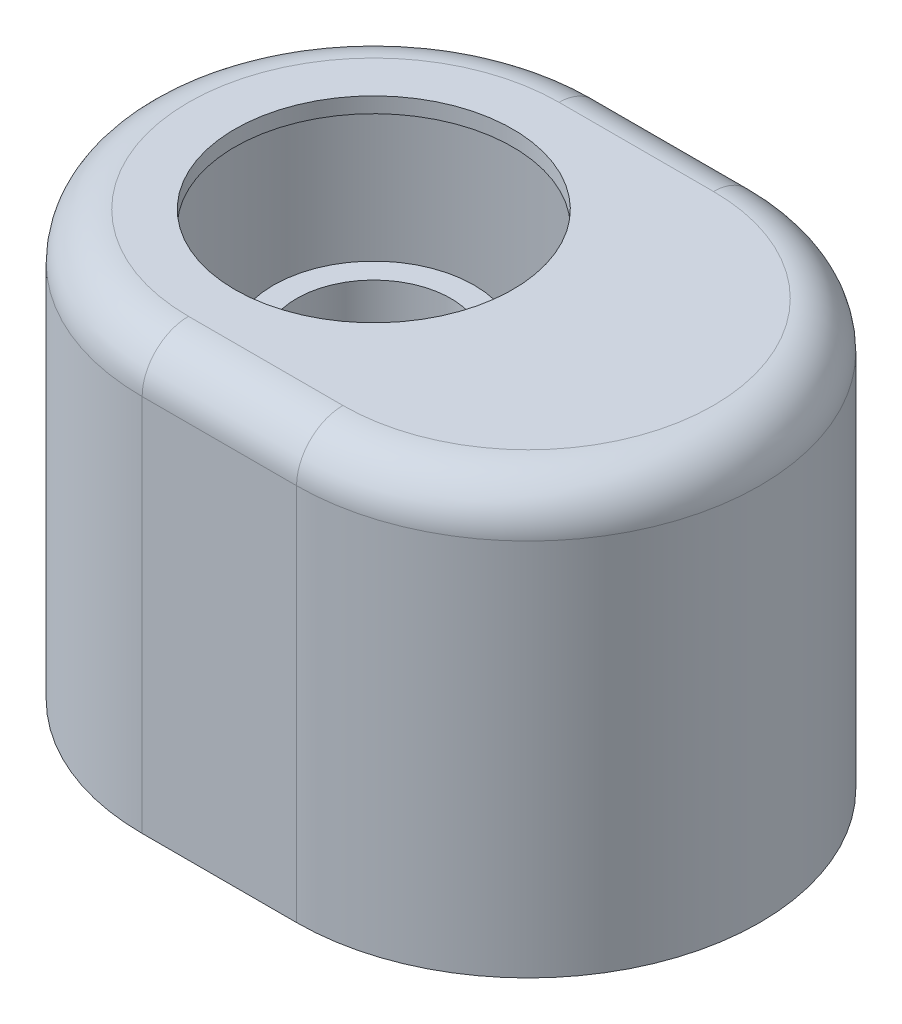
SolidWorks part; units mm, degrees
ref_plane "前视基准面" through (0, 0, 0) normal (0, 0, 1) x (1, 0, 0)
ref_plane "上视基准面" through (0, 0, 0) normal (0, 1, 0) x (1, 0, 0)
ref_plane "右视基准面" through (0, 0, 0) normal (1, 0, 0) x (0, 0, -1)
other "Configuration Table"
sketch "草图1" plane through (0, 0, 0) normal (0, 1, 0) x (1, 0, 0)
  line L0 (0, 0) -> (20, 0) construction
  line L1 (0, 30) -> (20, 30)
  line L2 (0, -30) -> (20, -30)
  arc A0 (0, 30) -> (0, -30) centre (0, 0) ccw
  arc A1 (20, -30) -> (20, 30) centre (20, 0) ccw
  point P3 (10, 0)
  dimension "D1" = 60
  dimension "D2" = 20
extrude "凸台-拉伸1" add sketch "草图1" along normal blind 55
fillet "圆角1" radius 6 4 edges at (10, 55, -30) (50, 55, 0) (10, 55, 30) (-30, 55, 0)
shell "抽壳1" thickness 2
sketch "草图2" plane through (0, 55, 0) normal (0, 1, 0) x (1, 0, 0)
  circle A0 centre (0, 0) radius 18
  dimension "D1" = 36
extrude "切除-拉伸1" cut sketch "草图2" against normal through all
sketch "草图3" plane through (0, 0, 0) normal (0, 0, 1) x (1, 0, 0)
  line L0 (0, 40) -> (0, 18.3692) construction
  line L1 (0, 49) -> (0, 0) construction
  line L2 (0, 40) -> (-10, 40) construction
  line L3 (-10, 40) -> (-13, 40)
  line L4 (-13, 40) -> (-13, 32.6329)
  line L5 (-13, 32.6329) -> (-9.5, 26.6329)
  line L6 (-9.5, 26.6329) -> (-9.5, 20)
  line L7 (-9.5, 20) -> (-6.5, 20)
  line L8 (-6.5, 20) -> (-6.5, 24)
  line L9 (-6.5, 24) -> (-4.5, 24)
  line L11 (-8, 32) -> (-8, 34)
  line L12 (-8, 34) -> (-10, 34)
  line L13 (-10, 34) -> (-10, 40)
  line L14 (-4.5, 24) -> (-4.5, 26)
  line L15 (-8, 32) -> (-4.5, 26)
  line L16 (18, 55) -> (-18, 55) construction
  point P7 (-9, 34)
  dimension "D1" = 13
  dimension "20" = 20
  dimension "D2" = 2
  dimension "D3" = 3
  dimension "D4" = 3
  dimension "D5" = 2
  dimension "D6" = 6
  dimension "D7" = 4
  dimension "D8" = 10
  dimension "D9" = 2
  dimension "D10" = 15
  dimension "D11" = 4
revolve "旋转1" add sketch "草图3" angle 360 about L0
